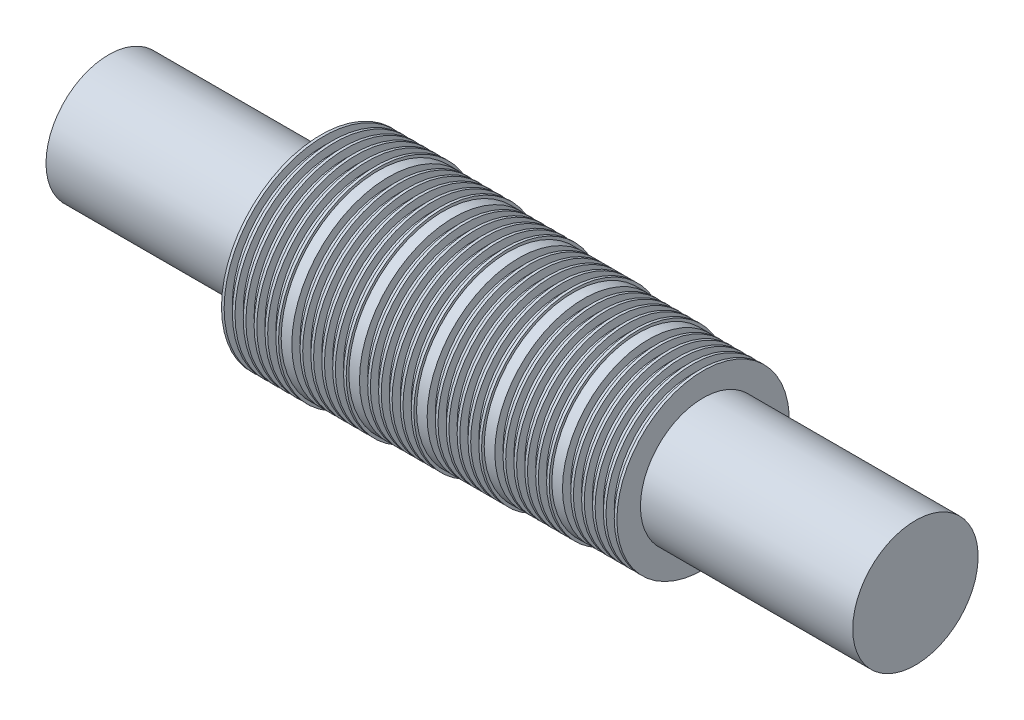
SolidWorks part; units mm, degrees
ref_plane "Front Plane" through (0, 0, 0) normal (0, 0, 1) x (1, 0, 0)
ref_plane "Top Plane" through (0, 0, 0) normal (0, 1, 0) x (1, 0, 0)
ref_plane "Right Plane" through (0, 0, 0) normal (1, 0, 0) x (0, 0, -1)
sketch "Sketch1" plane through (0, 0, 0) normal (0, 0, 1) x (1, 0, 0)
  line L24 (20.574, 9.525) -> (20.574, 8.7376)
  line L25 (20.574, 8.7376) -> (21.3614, 8.7376)
  line L26 (21.3614, 8.7376) -> (21.3614, 9.525)
  line L27 (21.3614, 9.525) -> (21.6154, 9.525)
  line L28 (21.6154, 9.525) -> (21.6154, 8.7376)
  line L29 (21.6154, 8.7376) -> (22.4028, 8.7376)
  line L30 (22.4028, 8.7376) -> (22.4028, 9.525)
  line L31 (22.4028, 9.525) -> (22.6568, 9.525)
  line L32 (22.6568, 9.525) -> (22.6568, 8.7376)
  line L33 (22.6568, 8.7376) -> (23.4442, 8.7376)
  line L34 (23.4442, 8.7376) -> (23.4442, 9.525)
  line L35 (23.4442, 9.525) -> (23.6982, 9.525)
  line L36 (23.6982, 9.525) -> (23.6982, 8.7376)
  line L37 (23.6982, 8.7376) -> (24.4856, 8.7376)
  line L38 (24.4856, 8.7376) -> (24.4856, 9.525)
  line L39 (24.4856, 9.525) -> (24.7396, 9.525)
  line L40 (24.7396, 9.525) -> (24.7396, 8.7376)
  line L41 (24.7396, 8.7376) -> (25.527, 8.7376)
  line L42 (25.527, 8.7376) -> (25.527, 9.525)
  line L43 (25.527, 9.525) -> (25.781, 9.525)
  line L44 (25.781, 9.525) -> (25.781, 9.271)
  line L45 (25.781, 9.271) -> (26.797, 9.271)
  line L46 (26.797, 9.271) -> (26.797, 8.4836)
  line L47 (26.797, 8.4836) -> (27.5844, 8.4836)
  line L48 (27.5844, 8.4836) -> (27.5844, 9.271)
  line L49 (27.5844, 9.271) -> (27.8384, 9.271)
  line L50 (27.8384, 9.271) -> (27.8384, 8.4836)
  line L51 (27.8384, 8.4836) -> (28.6258, 8.4836)
  line L52 (28.6258, 8.4836) -> (28.6258, 9.271)
  line L53 (28.6258, 9.271) -> (28.8798, 9.271)
  line L54 (28.8798, 9.271) -> (28.8798, 8.4836)
  line L55 (28.8798, 8.4836) -> (29.6672, 8.4836)
  line L56 (29.6672, 8.4836) -> (29.6672, 9.271)
  line L57 (29.6672, 9.271) -> (29.9212, 9.271)
  line L58 (29.9212, 9.271) -> (29.9212, 8.4836)
  line L59 (29.9212, 8.4836) -> (30.7086, 8.4836)
  line L60 (30.7086, 8.4836) -> (30.7086, 9.271)
  line L61 (30.7086, 9.271) -> (30.9626, 9.271)
  line L62 (30.9626, 9.271) -> (30.9626, 8.4836)
  line L63 (30.9626, 8.4836) -> (31.75, 8.4836)
  line L64 (31.75, 8.4836) -> (31.75, 9.271)
  line L65 (31.75, 9.271) -> (32.004, 9.271)
  line L66 (32.004, 9.271) -> (32.004, 9.017)
  line L67 (32.004, 9.017) -> (33.02, 9.017)
  line L68 (33.02, 9.017) -> (33.02, 8.2296)
  line L69 (33.02, 8.2296) -> (33.8074, 8.2296)
  line L70 (33.8074, 8.2296) -> (33.8074, 9.017)
  line L71 (33.8074, 9.017) -> (34.0614, 9.017)
  line L72 (34.0614, 9.017) -> (34.0614, 8.2296)
  line L73 (34.0614, 8.2296) -> (34.8488, 8.2296)
  line L74 (34.8488, 8.2296) -> (34.8488, 9.017)
  line L75 (34.8488, 9.017) -> (35.1028, 9.017)
  line L76 (35.1028, 9.017) -> (35.1028, 8.2296)
  line L77 (35.1028, 8.2296) -> (35.8902, 8.2296)
  line L78 (35.8902, 8.2296) -> (35.8902, 9.017)
  line L79 (35.8902, 9.017) -> (36.1442, 9.017)
  line L80 (36.1442, 9.017) -> (36.1442, 8.2296)
  line L81 (36.1442, 8.2296) -> (36.9316, 8.2296)
  line L82 (36.9316, 8.2296) -> (36.9316, 9.017)
  line L83 (36.9316, 9.017) -> (37.1856, 9.017)
  line L84 (37.1856, 9.017) -> (37.1856, 8.2296)
  line L85 (37.1856, 8.2296) -> (37.973, 8.2296)
  line L86 (37.973, 8.2296) -> (37.973, 9.017)
  line L87 (37.973, 9.017) -> (38.227, 9.017)
  line L88 (38.227, 9.017) -> (38.227, 8.763)
  line L89 (38.227, 8.763) -> (39.243, 8.763)
  line L90 (39.243, 8.763) -> (39.243, 7.9756)
  line L91 (39.243, 7.9756) -> (40.0304, 7.9756)
  line L92 (40.0304, 7.9756) -> (40.0304, 8.763)
  line L93 (40.0304, 8.763) -> (40.2844, 8.763)
  line L94 (40.2844, 8.763) -> (40.2844, 7.9756)
  line L95 (40.2844, 7.9756) -> (41.0718, 7.9756)
  line L96 (41.0718, 7.9756) -> (41.0718, 8.763)
  line L97 (41.0718, 8.763) -> (41.3258, 8.763)
  line L98 (41.3258, 8.763) -> (41.3258, 7.9756)
  line L99 (41.3258, 7.9756) -> (42.1132, 7.9756)
  line L100 (42.1132, 7.9756) -> (42.1132, 8.763)
  line L101 (42.1132, 8.763) -> (42.3672, 8.763)
  line L102 (42.3672, 8.763) -> (42.3672, 7.9756)
  line L103 (42.3672, 7.9756) -> (43.1546, 7.9756)
  line L104 (43.1546, 7.9756) -> (43.1546, 8.763)
  line L105 (43.1546, 8.763) -> (43.4086, 8.763)
  line L106 (43.4086, 8.763) -> (43.4086, 7.9756)
  line L107 (43.4086, 7.9756) -> (44.196, 7.9756)
  line L108 (44.196, 7.9756) -> (44.196, 8.763)
  line L109 (44.196, 8.763) -> (44.45, 8.763)
  line L110 (44.45, 8.763) -> (44.45, 8.509)
  line L111 (44.45, 8.509) -> (45.466, 8.509)
  line L112 (45.466, 8.509) -> (45.466, 7.7216)
  line L113 (45.466, 7.7216) -> (46.2534, 7.7216)
  line L114 (46.2534, 7.7216) -> (46.2534, 8.509)
  line L115 (46.2534, 8.509) -> (46.5074, 8.509)
  line L116 (46.5074, 8.509) -> (46.5074, 7.7216)
  line L117 (46.5074, 7.7216) -> (47.2948, 7.7216)
  line L118 (47.2948, 7.7216) -> (47.2948, 8.509)
  line L119 (47.2948, 8.509) -> (47.5488, 8.509)
  line L120 (47.5488, 8.509) -> (47.5488, 7.7216)
  line L121 (47.5488, 7.7216) -> (48.3362, 7.7216)
  line L122 (48.3362, 7.7216) -> (48.3362, 8.509)
  line L123 (48.3362, 8.509) -> (48.5902, 8.509)
  line L124 (48.5902, 8.509) -> (48.5902, 7.7216)
  line L125 (48.5902, 7.7216) -> (49.3776, 7.7216)
  line L126 (49.3776, 7.7216) -> (49.3776, 8.509)
  line L127 (49.3776, 8.509) -> (49.6316, 8.509)
  line L128 (49.6316, 8.509) -> (49.6316, 7.7216)
  line L129 (49.6316, 7.7216) -> (50.419, 7.7216)
  line L130 (50.419, 7.7216) -> (50.419, 8.509)
  line L131 (50.419, 8.509) -> (50.673, 8.509)
  line L132 (50.673, 8.509) -> (50.673, 8.255)
  line L133 (50.673, 8.255) -> (51.689, 8.255)
  line L134 (51.689, 8.255) -> (51.689, 7.4676)
  line L135 (51.689, 7.4676) -> (52.4764, 7.4676)
  line L136 (52.4764, 7.4676) -> (52.4764, 8.255)
  line L137 (52.4764, 8.255) -> (52.7304, 8.255)
  line L138 (52.7304, 8.255) -> (52.7304, 7.4676)
  line L139 (52.7304, 7.4676) -> (53.5178, 7.4676)
  line L140 (53.5178, 7.4676) -> (53.5178, 8.255)
  line L141 (53.5178, 8.255) -> (53.7718, 8.255)
  line L142 (53.7718, 8.255) -> (53.7718, 7.4676)
  line L143 (53.7718, 7.4676) -> (54.5592, 7.4676)
  line L144 (54.5592, 7.4676) -> (54.5592, 8.255)
  line L145 (54.5592, 8.255) -> (54.8132, 8.255)
  line L146 (54.8132, 8.255) -> (54.8132, 7.4676)
  line L147 (54.8132, 7.4676) -> (55.6006, 7.4676)
  line L148 (55.6006, 7.4676) -> (55.6006, 8.255)
  line L149 (55.6006, 8.255) -> (55.8546, 8.255)
  line L150 (55.8546, 8.255) -> (55.8546, 7.4676)
  line L151 (55.8546, 7.4676) -> (56.642, 7.4676)
  line L152 (56.642, 7.4676) -> (56.642, 8.255)
  line L153 (56.642, 8.255) -> (56.896, 8.255)
  line L156 (20.32, 6) -> (0, 6)
  line L157 (0, 6) -> (0, 0)
  line L158 (0, 0) -> (61.976, 0)
  line L160 (20.574, 9.525) -> (20.32, 9.525)
  line L161 (20.32, 9.525) -> (20.32, 6)
  line L162 (56.896, 6) -> (77.216, 6)
  line L163 (77.216, 6) -> (77.216, 0)
  line L164 (77.216, 0) -> (61.976, 0)
  line L165 (56.896, 8.255) -> (56.896, 6)
  point P5 (20.447, 9.525)
  point P6 (67.056, 6)
  dimension "D1" = 6
  dimension "D9" = 20.32
  dimension "D3" = 0.254
  dimension "D4" = 0.7874
  dimension "D5" = 0.7874
  dimension "D7" = 1.016
  dimension "D10" = 6
  dimension "D11" = 20.32
  dimension "D2" = 9.525
  dimension "D6" = 0.254
revolve "Revolve1" add sketch "Sketch1" angle 360 about L158
equation "\"kero_radius\"=0.23622in"
equation "\"D1@Sketch1\"=\"kero_radius\""
equation "\"lox_radius\"=0.23622in"
equation "\"Cavity_width\"=0.031in"
equation "\"tooth_width\"=0.01in"
equation "\"cavity_depth\"=0.031in"
equation "\"seal_step\"=0.01in"
equation "\"purge_length\"=0.04in"
equation "\"D3@Sketch1\"=\"tooth_width\""
equation "\"D4@Sketch1\"=\"Cavity_width\""
equation "\"D5@Sketch1\"=\"cavity_depth\""
equation "\"D7@Sketch1\"=\"purge_length\""
equation "\"D10@Sketch1\"=\"lox_radius\""
equation "\"lox_in_radius\"=.375in"
equation "\"bearing_radius\"= 0.629921"
equation "\"bearing_width\"=0.393701"
equation "\"insert_radius\" = 0.5925in"
equation "\"recycle_groove width\" = 0.05in"
equation "\"recycle_groove_depth\" = 0.04in"
equation "\"N2_purge_width\"= .05in"
equation "\"N2_purge_depth\"= .04in"
equation "\"drain_width\"= .05in"
equation "\"drain_depth\"= .04in"
equation "\"radial_clearance\"= .002in"
equation "\"IPS_flange_width\"= .25in"
equation "\"IPS_flange_radius\" = 2.2in"
equation "\"IPS_LOX_male_radius\"= .9in"
equation "\"IPS_Kero_male_radius\" = .9in"
equation "\"IPS_radius\"= 1.4in"
equation "\"InsertLength\"= 1.445in"
equation "\"D2@Sketch1\"=\"lox_in_radius\""
equation "\"D6@Sketch1\"=\"seal_step\""
